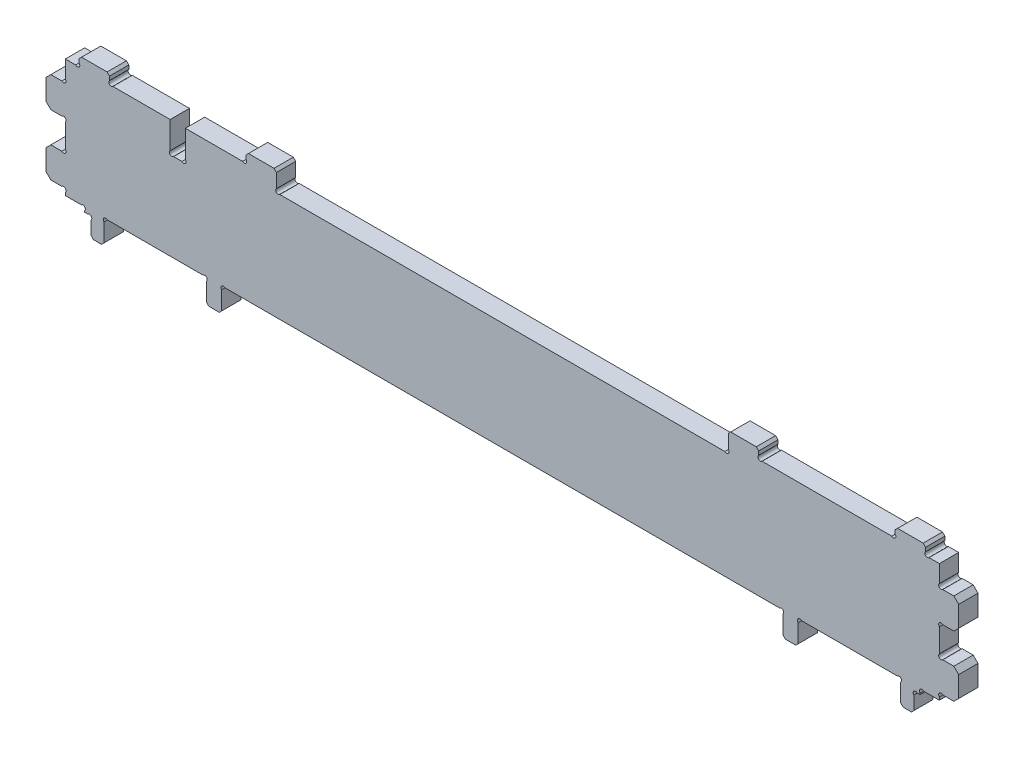
SolidWorks part; units mm, degrees
ref_plane "Front Plane" through (0, 0, 0) normal (0, 0, 1) x (1, 0, 0)
ref_plane "Top Plane" through (0, 0, 0) normal (0, 1, 0) x (1, 0, 0)
ref_plane "Right Plane" through (0, 0, 0) normal (1, 0, 0) x (0, 0, -1)
sketch "Sketch1" plane through (0, 0, 0) normal (0, 0, 1) x (1, 0, 0)
  line L69 (134.6215, -67.6125) -> (134.6215, -60.8103)
  line L70 (133.499, -59.6877) -> (102.0491, -59.6877)
  line L71 (100.9265, -60.8103) -> (100.9265, -67.6125)
  line L72 (100.9265, -67.6125) -> (95.9265, -67.6125)
  line L73 (95.9265, -67.6125) -> (95.9265, -60.8103)
  line L74 (94.804, -59.6877) -> (-87.4609, -59.6877)
  line L75 (-88.5835, -60.8103) -> (-88.5835, -67.6125)
  line L76 (-88.5835, -67.6125) -> (-93.5835, -67.6125)
  line L77 (-93.5835, -67.6125) -> (-93.5835, -60.8103)
  line L78 (-94.706, -59.6877) -> (-126.1559, -59.6877)
  line L79 (-127.2785, -60.8103) -> (-127.2785, -67.6125)
  line L80 (-127.2785, -67.6125) -> (-131.5077, -67.6125)
  line L81 (-131.5077, -67.6125) -> (-131.5077, -62.3851)
  line L82 (-132.6302, -61.2625) -> (-133.6285, -61.2625)
  line L83 (-133.6285, -61.2625) -> (-133.6285, -60.8103)
  line L84 (-134.751, -59.6877) -> (-139.9785, -59.6877)
  line L85 (-139.9785, -59.6877) -> (-139.9785, -58.7351)
  line L86 (-141.101, -57.6125) -> (-146.3285, -57.6125)
  line L87 (-146.3285, -57.6125) -> (-146.3285, -47.6125)
  line L88 (-146.3285, -47.6125) -> (-141.101, -47.6125)
  line L89 (-139.9785, -46.49) -> (-139.9785, -38.7351)
  line L90 (-141.101, -37.6125) -> (-146.3285, -37.6125)
  line L91 (-146.3285, -37.6125) -> (-146.3285, -27.6125)
  line L92 (-146.3285, -27.6125) -> (-141.101, -27.6125)
  line L93 (-139.9785, -26.49) -> (-139.9785, -20.7875)
  line L94 (-139.9785, -20.7875) -> (-136.576, -20.7875)
  line L95 (-135.4535, -19.665) -> (-135.4535, -17.6125)
  line L96 (-135.4535, -17.6125) -> (-125.4535, -17.6125)
  line L97 (-125.4535, -17.6125) -> (-125.4535, -19.665)
  line L98 (-124.3309, -20.7875) -> (-105.5215, -20.7875)
  line L99 (-105.5215, -20.7875) -> (-105.5215, -29.665)
  line L100 (-104.3989, -30.7875) -> (-101.644, -30.7875)
  line L101 (-100.5215, -29.665) -> (-100.5215, -20.7875)
  line L102 (-100.5215, -20.7875) -> (-81.712, -20.7875)
  line L103 (-80.5895, -19.665) -> (-80.5895, -17.6125)
  line L104 (-80.5895, -17.6125) -> (-70.5895, -17.6125)
  line L105 (-70.5895, -17.6125) -> (-70.5895, -23.0052)
  line L106 (-69.4669, -24.1277) -> (76.81, -24.1277)
  line L107 (77.9325, -23.0052) -> (77.9325, -17.6125)
  line L108 (77.9325, -17.6125) -> (87.9325, -17.6125)
  line L109 (87.9325, -17.6125) -> (87.9325, -19.665)
  line L110 (89.0551, -20.7875) -> (131.674, -20.7875)
  line L111 (132.7965, -19.665) -> (132.7965, -17.6125)
  line L112 (132.7965, -17.6125) -> (142.7965, -17.6125)
  line L113 (142.7965, -17.6125) -> (142.7965, -19.665)
  line L114 (143.9191, -20.7875) -> (147.3215, -20.7875)
  line L115 (147.3215, -20.7875) -> (147.3215, -26.49)
  line L116 (148.4441, -27.6125) -> (153.6715, -27.6125)
  line L117 (153.6715, -27.6125) -> (153.6715, -37.6125)
  line L118 (153.6715, -37.6125) -> (148.4441, -37.6125)
  line L119 (147.3215, -38.7351) -> (147.3215, -46.49)
  line L120 (148.4441, -47.6125) -> (153.6715, -47.6125)
  line L121 (153.6715, -47.6125) -> (153.6715, -57.6125)
  line L122 (153.6715, -57.6125) -> (148.4441, -57.6125)
  line L123 (147.3215, -58.7351) -> (147.3215, -59.6877)
  line L124 (147.3215, -59.6877) -> (142.0941, -59.6877)
  line L125 (140.9715, -60.8103) -> (140.9715, -61.2625)
  line L126 (140.9715, -61.2625) -> (140.0715, -61.2625)
  line L127 (138.949, -62.3851) -> (138.949, -67.6125)
  line L128 (138.949, -67.6125) -> (134.6215, -67.6125)
  arc A28 (134.6215, -60.8103) -> (133.499, -59.6877) centre (134.0603, -60.249) ccw
  arc A29 (102.0491, -59.6877) -> (100.9265, -60.8103) centre (101.4878, -60.249) ccw
  arc A30 (95.9265, -60.8103) -> (94.804, -59.6877) centre (95.3653, -60.249) ccw
  arc A31 (-87.4609, -59.6877) -> (-88.5835, -60.8103) centre (-88.0222, -60.249) ccw
  arc A32 (-93.5835, -60.8103) -> (-94.706, -59.6877) centre (-94.1447, -60.249) ccw
  arc A33 (-126.1559, -59.6877) -> (-127.2785, -60.8103) centre (-126.7172, -60.249) ccw
  arc A34 (-131.5077, -62.3851) -> (-132.6302, -61.2625) centre (-132.069, -61.8238) ccw
  arc A35 (-133.6285, -60.8103) -> (-134.751, -59.6877) centre (-134.1897, -60.249) ccw
  arc A36 (-139.9785, -58.7351) -> (-141.101, -57.6125) centre (-140.5397, -58.1738) ccw
  arc A37 (-141.101, -47.6125) -> (-139.9785, -46.49) centre (-140.5397, -47.0513) ccw
  arc A38 (-139.9785, -38.7351) -> (-141.101, -37.6125) centre (-140.5397, -38.1738) ccw
  arc A39 (-141.101, -27.6125) -> (-139.9785, -26.49) centre (-140.5397, -27.0513) ccw
  arc A40 (-136.576, -20.7875) -> (-135.4535, -19.665) centre (-136.0147, -20.2263) ccw
  arc A41 (-125.4535, -19.665) -> (-124.3309, -20.7875) centre (-124.8922, -20.2263) ccw
  arc A42 (-105.5215, -29.665) -> (-104.3989, -30.7875) centre (-104.9602, -30.2263) ccw
  arc A43 (-101.644, -30.7875) -> (-100.5215, -29.665) centre (-101.0827, -30.2263) ccw
  arc A44 (-81.712, -20.7875) -> (-80.5895, -19.665) centre (-81.1507, -20.2263) ccw
  arc A45 (-70.5895, -23.0052) -> (-69.4669, -24.1277) centre (-70.0282, -23.5665) ccw
  arc A46 (76.81, -24.1277) -> (77.9325, -23.0052) centre (77.3713, -23.5665) ccw
  arc A47 (87.9325, -19.665) -> (89.0551, -20.7875) centre (88.4938, -20.2263) ccw
  arc A48 (131.674, -20.7875) -> (132.7965, -19.665) centre (132.2353, -20.2263) ccw
  arc A49 (142.7965, -19.665) -> (143.9191, -20.7875) centre (143.3578, -20.2263) ccw
  arc A50 (147.3215, -26.49) -> (148.4441, -27.6125) centre (147.8828, -27.0513) ccw
  arc A51 (148.4441, -37.6125) -> (147.3215, -38.7351) centre (147.8828, -38.1738) ccw
  arc A52 (147.3215, -46.49) -> (148.4441, -47.6125) centre (147.8828, -47.0513) ccw
  arc A53 (148.4441, -57.6125) -> (147.3215, -58.7351) centre (147.8828, -58.1738) ccw
  arc A54 (142.0941, -59.6877) -> (140.9715, -60.8103) centre (141.5328, -60.249) ccw
  arc A55 (140.0715, -61.2625) -> (138.949, -62.3851) centre (139.5102, -61.8238) ccw
  point P244 (0, 0)
extrude "Boss-Extrude1" add sketch "Sketch1" along normal blind 6.35
chamfer "Chamfer1" distance 0.7937 angle 45 16 edges at (-131.5077, -67.6125, 3.175) (-93.5835, -67.6125, 3.175) (-127.2785, -67.6125, 3.175) (-88.5835, -67.6125, 3.175) (100.9265, -67.6125, 3.175) (95.9265, -67.6125, 3.175) (134.6215, -67.6125, 3.175) (138.949, -67.6125, 3.175) (132.7965, -17.6125, 3.175) (142.7965, -17.6125, 3.175) (87.9325, -17.6125, 3.175) (77.9325, -17.6125, 3.175) (-70.5895, -17.6125, 3.175) (-80.5895, -17.6125, 3.175) (-125.4535, -17.6125, 3.175) (-135.4535, -17.6125, 3.175)
chamfer "Chamfer2" distance 1.5875 angle 45 8 edges at (153.6715, -57.6125, 3.175) (153.6715, -47.6125, 3.175) (153.6715, -37.6125, 3.175) (153.6715, -27.6125, 3.175) (-146.3285, -57.6125, 3.175) (-146.3285, -47.6125, 3.175) (-146.3285, -37.6125, 3.175) (-146.3285, -27.6125, 3.175)
